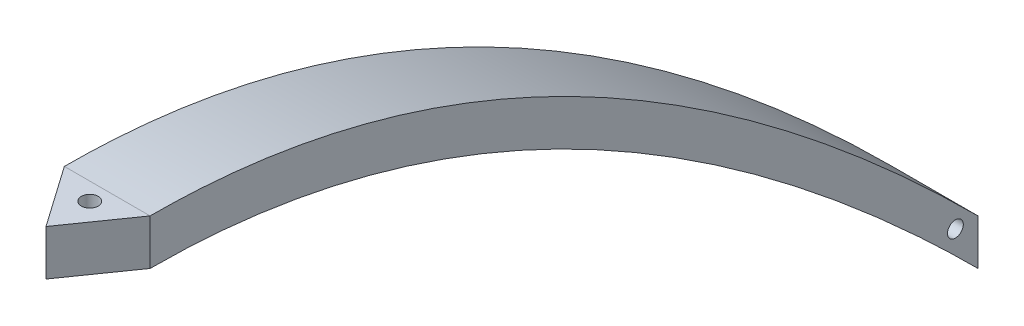
SolidWorks part; units mm, degrees
other "Markup1"
sketch "Sketch3" plane through (0, 5.588, -101.6) normal (0, 1, 0) x (1, 0, 0)
ref_plane "Front Plane" through (0, 0, 0) normal (0, 0, 1) x (1, 0, 0)
ref_plane "Top Plane" through (0, 0, 0) normal (0, 1, 0) x (1, 0, 0)
ref_plane "Right Plane" through (0, 0, 0) normal (1, 0, 0) x (0, 0, -1)
sketch "Sketch1" plane through (0, 0, 0) normal (1, 0, 0) x (0, 0, -1)
  line L0 (0, 0) -> (0, 5.588)
  line L1 (101.6, -50.8) -> (101.6, -45.212)
  spline S0 degree 2 poles (-10.16, -0.508) (49.7682, 5.4848) (109.6965, -59.2191) knots 0 0 0 1 1 1 construction
  spline S1 degree 2 poles (0, 0) (50.8, 0) (101.6, -50.8) knots 0.084768 0.084768 0.084768 0.932448 0.932448 0.932448
  spline S2 degree 2 poles (-10.16, 5.08) (49.7682, 11.0728) (109.6965, -53.6311) knots 0 0 0 1 1 1 construction
  spline S3 degree 2 poles (0, 5.588) (50.8, 5.588) (101.6, -45.212) knots 0.084768 0.084768 0.084768 0.932448 0.932448 0.932448
  point P10 (0, 0)
  point P11 (0, 0)
  point P13 (0, 0)
  point P14 (0, 0)
  dimension "D1" = 101.6
  dimension "D2" = 5.588
extrude "Boss-Extrude1" add sketch "Sketch1" along normal blind 10.5207
sketch "Sketch2" plane through (0, 0, 0) normal (0, 1, 0) x (1, 0, 0)
  line L0 (0, 0) -> (10.5207, 0)
  line L1 (10.5207, 0) -> (5.2603, -7.5125)
  line L2 (5.2603, -7.5125) -> (0, 0)
  dimension "D1" = 55
  dimension "D2" = 55
extrude "Boss-Extrude3" add sketch "Sketch2" along normal up to vertex (5.588 mm away)
sketch "Sketch4" plane through (0, 5.588, 0) normal (0, 1, 0) x (1, 0, 0)
  line L0 (5.2603, -7.5125) -> (5.2603, 0) construction
  line L1 (10.5207, 0) -> (0, 0) construction
  circle A0 centre (5.2603, -2.1373) radius 1.0371
  dimension "D1" = 2.1373
  dimension "D2" = 2.0742
extrude "Cut-Extrude1" cut sketch "Sketch4" against normal up to surface (5.588 mm away) up to face at (5.2603, 0, 2.5042)
sketch "Sketch5" plane through (0, 0, 0) normal (-1, 0, 0) x (0, 0, 1)
  line L0 (-101.6, -45.212) -> (-98.826, -48.0639) construction
  circle A0 centre (-98.826, -45.212) radius 0.9705
  parabola Q18 (0, 0) -> (-101.6, -50.8) focus (0, -50.8) apex (0, 0) construction
  dimension "D1" = 1.9409
  dimension "D2" = 1.9885
  dimension "D3" = 3.9785
  dimension "D4" = 2.8519
extrude "Cut-Extrude2" cut sketch "Sketch5" against normal up to surface (10.5207 mm away) up to face at (10.5207, -22.606, -50.8)
